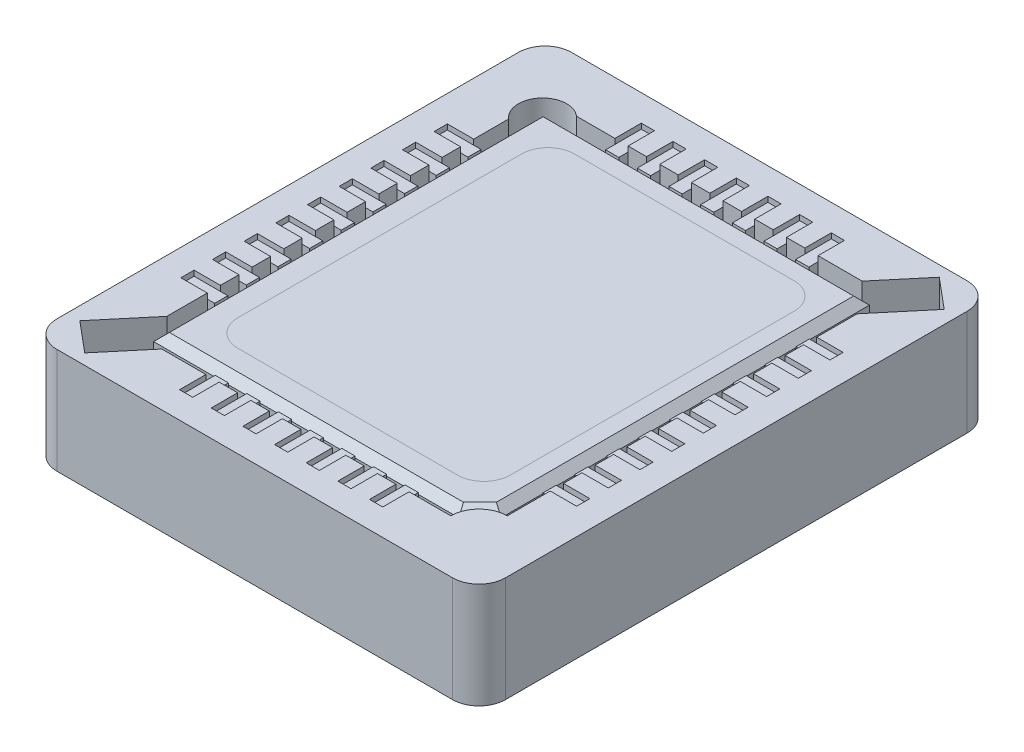
SolidWorks part; units mm, degrees
ref_plane "Alzado" through (0, 0, 0) normal (0, 0, 1) x (1, 0, 0)
ref_plane "Planta" through (0, 0, 0) normal (0, 1, 0) x (1, 0, 0)
ref_plane "Vista lateral" through (0, 0, 0) normal (1, 0, 0) x (0, 0, -1)
sketch "Croquis1" plane through (0, 0, 0) normal (0, 1, 0) x (1, 0, 0)
  line L0 (-6.5, -6.5829) -> (-8.0038, -8.3759)
  line L1 (-7.5, 9.75) -> (7.5, 9.75)
  line L2 (-8.5, 8.75) -> (-8.5, -8.75)
  line L3 (-7.5, -9.75) -> (7.5, -9.75)
  line L4 (8.5, 8.75) -> (8.5, -8.75)
  line L5 (-5.304, 7.75) -> (5.5211, 7.75)
  line L6 (-6.5, 6.3718) -> (-6.5, -6.5829)
  line L7 (-5.5211, -7.75) -> (5.4294, -7.75)
  line L8 (6.5, 6.5829) -> (6.5, -6.6794)
  line L9 (6.8545, 9.3398) -> (5.5211, 7.75)
  line L10 (8.0038, 8.3759) -> (6.5, 6.5829)
  line L11 (6.8545, 9.3398) -> (8.0038, 8.3759)
  line L12 (0, 0) -> (2.3031, -1.9317) construction
  line L13 (-8.0038, -8.3759) -> (-6.8545, -9.3398)
  line L14 (-5.5211, -7.75) -> (-6.8545, -9.3398)
  arc A0 (-7.5, 9.75) -> (-8.5, 8.75) centre (-7.5, 8.75) ccw
  arc A1 (7.5, 9.75) -> (8.5, 8.75) centre (7.5, 8.75) cw
  arc A2 (7.5, -9.75) -> (8.5, -8.75) centre (7.5, -8.75) ccw
  arc A3 (-8.5, -8.75) -> (-7.5, -9.75) centre (-7.5, -8.75) ccw
  arc A4 (6.5, -6.6794) -> (5.4294, -7.75) centre (6.5, -7.75) ccw
  arc A5 (-5.304, 7.75) -> (-6.5, 6.3718) centre (-5.902, 7.0609) ccw
  point P6 (-8.5, 9.75)
  point P9 (8.5, 9.75)
  point P14 (-8.5, -9.75)
  dimension "D5" = 1
  dimension "D1" = 17
  dimension "D2" = 19.5
  dimension "D3" = 8.5
  dimension "D4" = 9.75
  dimension "D6" = 2
  dimension "D7" = 2
  dimension "D8" = 2
  dimension "D9" = 2
  dimension "D12" = 90
extrude "Extruir1" add sketch "Croquis1" along normal blind 4
sketch "Croquis3" plane through (0, 4, 0) normal (0, 1, 0) x (-1, 0, 0)
  line L0 (-6.1479, 6.5628) -> (-5.3479, 7.3628)
  line L1 (-6.1479, -7.3996) -> (6.2216, -7.3996)
  line L2 (-6.1479, -7.3996) -> (-6.1479, 6.5628)
  line L3 (-5.3479, 7.3628) -> (6.2216, 7.3628)
  line L4 (6.2216, -7.3996) -> (6.2216, 7.3628)
  point P6 (-6.1479, 7.3628)
  dimension "D1" = 0.8
  dimension "D2" = 45
extrude "Extruir2" add sketch "Croquis3" against normal blind 4 separate body
chamfer "Chaflán1" distance 0.3 angle 45 5 edges at (-6.2216, 4, -0.0184) (-0.0368, 4, -7.3996) (6.1479, 4, -0.4184) (5.7479, 4, 6.9628) (-0.4368, 4, 7.3628)
sketch "Croquis4" plane through (0, 4, 0) normal (0, 1, 0) x (-1, 0, 0)
  line L1 (-4.2199, -6.4713) -> (4.1071, -6.4713)
  line L2 (-5.2199, -5.4713) -> (-5.2199, 5.2855)
  line L3 (-4.2199, 6.2855) -> (4.1071, 6.2855)
  line L4 (5.1071, -5.4713) -> (5.1071, 5.2855)
  arc A0 (-4.2199, -6.4713) -> (-5.2199, -5.4713) centre (-4.2199, -5.4713) cw
  arc A1 (-5.2199, 5.2855) -> (-4.2199, 6.2855) centre (-4.2199, 5.2855) cw
  arc A2 (4.1071, -6.4713) -> (5.1071, -5.4713) centre (4.1071, -5.4713) ccw
  arc A3 (4.1071, 6.2855) -> (5.1071, 5.2855) centre (4.1071, 5.2855) cw
  dimension "D1" = 1
split line "Línea de partición1"
sketch "Croquis5" plane through (0, 4, 0) normal (0, 1, 0) x (1, 0, 0)
  line L0 (6.5, -6.6794) -> (6.5, 6.5829) construction
  line L1 (6.5, 0.25) -> (7.5, 0.25)
  line L2 (6.5, 0.25) -> (6.5, -0.25)
  line L3 (6.5, -0.25) -> (7.5, -0.25)
  line L4 (7.5, 0.25) -> (7.5, -0.25)
  line L5 (8.5, 0) -> (10.2177, 0) construction
  line L6 (8.5, -8.75) -> (8.5, 8.75) construction
  line L7 (6.5, 1.45) -> (7.5, 1.45)
  line L8 (6.5, 1.45) -> (6.5, 0.95)
  line L9 (6.5, 0.95) -> (7.5, 0.95)
  line L10 (7.5, 1.45) -> (7.5, 0.95)
  line L11 (6.5, 2.65) -> (7.5, 2.65)
  line L12 (6.5, 2.65) -> (6.5, 2.15)
  line L13 (6.5, 2.15) -> (7.5, 2.15)
  line L14 (7.5, 2.65) -> (7.5, 2.15)
  line L15 (6.5, 3.85) -> (7.5, 3.85)
  line L16 (6.5, 3.85) -> (6.5, 3.35)
  line L17 (6.5, 3.35) -> (7.5, 3.35)
  line L18 (7.5, 3.85) -> (7.5, 3.35)
  line L19 (6.5, 5.05) -> (7.5, 5.05)
  line L20 (6.5, 5.05) -> (6.5, 4.55)
  line L21 (6.5, 4.55) -> (7.5, 4.55)
  line L22 (7.5, 5.05) -> (7.5, 4.55)
  line L23 (7.5, -5.05) -> (7.5, -4.55)
  line L24 (6.5, -4.55) -> (7.5, -4.55)
  line L25 (6.5, -5.05) -> (6.5, -4.55)
  line L26 (6.5, -5.05) -> (7.5, -5.05)
  line L27 (7.5, -3.85) -> (7.5, -3.35)
  line L28 (6.5, -3.35) -> (7.5, -3.35)
  line L29 (6.5, -3.85) -> (6.5, -3.35)
  line L30 (6.5, -3.85) -> (7.5, -3.85)
  line L31 (7.5, -2.65) -> (7.5, -2.15)
  line L32 (6.5, -2.15) -> (7.5, -2.15)
  line L33 (6.5, -2.65) -> (6.5, -2.15)
  line L34 (6.5, -2.65) -> (7.5, -2.65)
  line L35 (7.5, -1.45) -> (7.5, -0.95)
  line L36 (6.5, -0.95) -> (7.5, -0.95)
  line L37 (6.5, -1.45) -> (6.5, -0.95)
  line L38 (6.5, -1.45) -> (7.5, -1.45)
  line L39 (0, 9.75) -> (0, 11.4117) construction
  line L40 (7.5, 9.75) -> (-7.5, 9.75) construction
  line L41 (-6.5, -1.45) -> (-7.5, -1.45)
  line L42 (-6.5, -1.45) -> (-6.5, -0.95)
  line L43 (-6.5, -0.95) -> (-7.5, -0.95)
  line L44 (-7.5, -1.45) -> (-7.5, -0.95)
  line L45 (-6.5, -2.65) -> (-7.5, -2.65)
  line L46 (-6.5, -2.65) -> (-6.5, -2.15)
  line L47 (-6.5, -2.15) -> (-7.5, -2.15)
  line L48 (-7.5, -2.65) -> (-7.5, -2.15)
  line L49 (-6.5, -3.85) -> (-7.5, -3.85)
  line L50 (-6.5, -3.85) -> (-6.5, -3.35)
  line L51 (-6.5, -3.35) -> (-7.5, -3.35)
  line L52 (-7.5, -3.85) -> (-7.5, -3.35)
  line L53 (-6.5, -5.05) -> (-7.5, -5.05)
  line L54 (-6.5, -5.05) -> (-6.5, -4.55)
  line L55 (-6.5, -4.55) -> (-7.5, -4.55)
  line L56 (-7.5, -5.05) -> (-7.5, -4.55)
  line L57 (-7.5, 5.05) -> (-7.5, 4.55)
  line L58 (-6.5, 4.55) -> (-7.5, 4.55)
  line L59 (-6.5, 5.05) -> (-6.5, 4.55)
  line L60 (-6.5, 5.05) -> (-7.5, 5.05)
  line L61 (-7.5, 3.85) -> (-7.5, 3.35)
  line L62 (-6.5, 3.35) -> (-7.5, 3.35)
  line L63 (-6.5, 3.85) -> (-6.5, 3.35)
  line L64 (-6.5, 3.85) -> (-7.5, 3.85)
  line L65 (-7.5, 2.65) -> (-7.5, 2.15)
  line L66 (-6.5, 2.15) -> (-7.5, 2.15)
  line L67 (-6.5, 2.65) -> (-6.5, 2.15)
  line L68 (-6.5, 2.65) -> (-7.5, 2.65)
  line L69 (-7.5, 1.45) -> (-7.5, 0.95)
  line L70 (-6.5, 0.95) -> (-7.5, 0.95)
  line L71 (-6.5, 1.45) -> (-6.5, 0.95)
  line L72 (-6.5, 1.45) -> (-7.5, 1.45)
  line L73 (-7.5, 0.25) -> (-7.5, -0.25)
  line L74 (-6.5, -0.25) -> (-7.5, -0.25)
  line L75 (-6.5, 0.25) -> (-6.5, -0.25)
  line L76 (-6.5, 0.25) -> (-7.5, 0.25)
  line L77 (5.5211, 7.75) -> (-5.304, 7.75) construction
  line L78 (-0.25, 7.75) -> (0.25, 7.75)
  line L79 (-0.25, 7.75) -> (-0.25, 8.75)
  line L80 (-0.25, 8.75) -> (0.25, 8.75)
  line L81 (0.25, 7.75) -> (0.25, 8.75)
  line L82 (0.95, 7.75) -> (1.45, 7.75)
  line L83 (0.95, 7.75) -> (0.95, 8.75)
  line L84 (0.95, 8.75) -> (1.45, 8.75)
  line L85 (1.45, 7.75) -> (1.45, 8.75)
  line L86 (2.15, 7.75) -> (2.65, 7.75)
  line L87 (2.15, 7.75) -> (2.15, 8.75)
  line L88 (2.15, 8.75) -> (2.65, 8.75)
  line L89 (2.65, 7.75) -> (2.65, 8.75)
  line L90 (3.35, 7.75) -> (3.85, 7.75)
  line L91 (3.35, 7.75) -> (3.35, 8.75)
  line L92 (3.35, 8.75) -> (3.85, 8.75)
  line L93 (3.85, 7.75) -> (3.85, 8.75)
  line L94 (-3.85, 7.75) -> (-3.85, 8.75)
  line L95 (-3.35, 8.75) -> (-3.85, 8.75)
  line L96 (-3.35, 7.75) -> (-3.35, 8.75)
  line L97 (-3.35, 7.75) -> (-3.85, 7.75)
  line L98 (-2.65, 7.75) -> (-2.65, 8.75)
  line L99 (-2.15, 8.75) -> (-2.65, 8.75)
  line L100 (-2.15, 7.75) -> (-2.15, 8.75)
  line L101 (-2.15, 7.75) -> (-2.65, 7.75)
  line L102 (-1.45, 7.75) -> (-1.45, 8.75)
  line L103 (-0.95, 8.75) -> (-1.45, 8.75)
  line L104 (-0.95, 7.75) -> (-0.95, 8.75)
  line L105 (-0.95, 7.75) -> (-1.45, 7.75)
  line L106 (-0.95, -7.75) -> (-1.45, -7.75)
  line L107 (-0.95, -7.75) -> (-0.95, -8.75)
  line L108 (-0.95, -8.75) -> (-1.45, -8.75)
  line L109 (-1.45, -7.75) -> (-1.45, -8.75)
  line L110 (-2.15, -7.75) -> (-2.65, -7.75)
  line L111 (-2.15, -7.75) -> (-2.15, -8.75)
  line L112 (-2.15, -8.75) -> (-2.65, -8.75)
  line L113 (-2.65, -7.75) -> (-2.65, -8.75)
  line L114 (-3.35, -7.75) -> (-3.85, -7.75)
  line L115 (-3.35, -7.75) -> (-3.35, -8.75)
  line L116 (-3.35, -8.75) -> (-3.85, -8.75)
  line L117 (-3.85, -7.75) -> (-3.85, -8.75)
  line L118 (3.85, -7.75) -> (3.85, -8.75)
  line L119 (3.35, -8.75) -> (3.85, -8.75)
  line L120 (3.35, -7.75) -> (3.35, -8.75)
  line L121 (3.35, -7.75) -> (3.85, -7.75)
  line L122 (2.65, -7.75) -> (2.65, -8.75)
  line L123 (2.15, -8.75) -> (2.65, -8.75)
  line L124 (2.15, -7.75) -> (2.15, -8.75)
  line L125 (2.15, -7.75) -> (2.65, -7.75)
  line L126 (1.45, -7.75) -> (1.45, -8.75)
  line L127 (0.95, -8.75) -> (1.45, -8.75)
  line L128 (0.95, -7.75) -> (0.95, -8.75)
  line L129 (0.95, -7.75) -> (1.45, -7.75)
  line L130 (0.25, -7.75) -> (0.25, -8.75)
  line L131 (-0.25, -8.75) -> (0.25, -8.75)
  line L132 (-0.25, -7.75) -> (-0.25, -8.75)
  line L133 (-0.25, -7.75) -> (0.25, -7.75)
  dimension "D1" = 0.5
  dimension "D2" = 0.25
  dimension "D3" = 1
  dimension "D4" = 1
  dimension "D5" = 0.5
  dimension "D6" = 0.25
extrude "Cortar-Extruir1" cut sketch "Croquis5" against normal blind 3
sketch "Croquis6" plane through (0, 1, 0) normal (0, 1, 0) x (1, 0, 0)
  line L0 (-6.2216, 7.3996) -> (6.1479, 7.3996) construction
  line L1 (-3.85, 8.75) -> (-3.35, 8.75)
  line L2 (-3.85, 8.75) -> (-3.85, 7.3996)
  line L3 (-3.85, 7.3996) -> (-3.35, 7.3996)
  line L4 (-3.35, 8.75) -> (-3.35, 7.3996)
  line L5 (-2.65, 8.75) -> (-2.15, 8.75)
  line L6 (-2.65, 8.75) -> (-2.65, 7.3996)
  line L7 (-2.65, 7.3996) -> (-2.15, 7.3996)
  line L8 (-2.15, 8.75) -> (-2.15, 7.3996)
  line L9 (-1.45, 8.75) -> (-0.95, 8.75)
  line L10 (-1.45, 8.75) -> (-1.45, 7.3996)
  line L11 (-1.45, 7.3996) -> (-0.95, 7.3996)
  line L12 (-0.95, 8.75) -> (-0.95, 7.3996)
  line L13 (-0.25, 8.75) -> (0.25, 8.75)
  line L14 (-0.25, 8.75) -> (-0.25, 7.3996)
  line L15 (-0.25, 7.3996) -> (0.25, 7.3996)
  line L16 (0.25, 8.75) -> (0.25, 7.3996)
  line L17 (0.95, 8.75) -> (1.45, 8.75)
  line L18 (0.95, 8.75) -> (0.95, 7.3996)
  line L19 (0.95, 7.3996) -> (1.45, 7.3996)
  line L20 (1.45, 8.75) -> (1.45, 7.3996)
  line L21 (2.15, 8.75) -> (2.65, 8.75)
  line L22 (2.15, 8.75) -> (2.15, 7.3996)
  line L23 (2.15, 7.3996) -> (2.65, 7.3996)
  line L24 (2.65, 8.75) -> (2.65, 7.3996)
  line L25 (3.35, 8.75) -> (3.85, 8.75)
  line L26 (3.35, 8.75) -> (3.35, 7.3996)
  line L27 (3.35, 7.3996) -> (3.85, 7.3996)
  line L28 (3.85, 8.75) -> (3.85, 7.3996)
  line L29 (8.5, 0) -> (11.2679, 0) construction
  line L30 (8.5, -8.75) -> (8.5, 8.75) construction
  line L31 (3.85, -8.75) -> (3.85, -7.3996)
  line L32 (3.35, -7.3996) -> (3.85, -7.3996)
  line L33 (3.35, -8.75) -> (3.35, -7.3996)
  line L34 (3.35, -8.75) -> (3.85, -8.75)
  line L35 (2.65, -8.75) -> (2.65, -7.3996)
  line L36 (2.15, -7.3996) -> (2.65, -7.3996)
  line L37 (2.15, -8.75) -> (2.15, -7.3996)
  line L38 (2.15, -8.75) -> (2.65, -8.75)
  line L39 (1.45, -8.75) -> (1.45, -7.3996)
  line L40 (0.95, -7.3996) -> (1.45, -7.3996)
  line L41 (0.95, -8.75) -> (0.95, -7.3996)
  line L42 (0.95, -8.75) -> (1.45, -8.75)
  line L43 (0.25, -8.75) -> (0.25, -7.3996)
  line L44 (-0.25, -7.3996) -> (0.25, -7.3996)
  line L45 (-0.25, -8.75) -> (-0.25, -7.3996)
  line L46 (-0.25, -8.75) -> (0.25, -8.75)
  line L47 (-0.95, -8.75) -> (-0.95, -7.3996)
  line L48 (-1.45, -7.3996) -> (-0.95, -7.3996)
  line L49 (-1.45, -8.75) -> (-1.45, -7.3996)
  line L50 (-1.45, -8.75) -> (-0.95, -8.75)
  line L51 (-2.15, -8.75) -> (-2.15, -7.3996)
  line L52 (-2.65, -7.3996) -> (-2.15, -7.3996)
  line L53 (-2.65, -8.75) -> (-2.65, -7.3996)
  line L54 (-2.65, -8.75) -> (-2.15, -8.75)
  line L55 (-3.35, -8.75) -> (-3.35, -7.3996)
  line L56 (-3.85, -7.3996) -> (-3.35, -7.3996)
  line L57 (-3.85, -8.75) -> (-3.85, -7.3996)
  line L58 (-3.85, -8.75) -> (-3.35, -8.75)
  line L59 (-6.2216, -7.3628) -> (-6.2216, 7.3996) construction
  line L60 (-7.5, 5.05) -> (-6.2216, 5.05)
  line L61 (-7.5, 5.05) -> (-7.5, 4.55)
  line L62 (-7.5, 4.55) -> (-6.2216, 4.55)
  line L63 (-6.2216, 5.05) -> (-6.2216, 4.55)
  line L64 (-7.5, 3.85) -> (-6.2216, 3.85)
  line L65 (-7.5, 3.85) -> (-7.5, 3.35)
  line L66 (-7.5, 3.35) -> (-6.2216, 3.35)
  line L67 (-6.2216, 3.85) -> (-6.2216, 3.35)
  line L68 (-7.5, 2.65) -> (-6.2216, 2.65)
  line L69 (-7.5, 2.65) -> (-7.5, 2.15)
  line L70 (-7.5, 2.15) -> (-6.2216, 2.15)
  line L71 (-6.2216, 2.65) -> (-6.2216, 2.15)
  line L72 (-7.5, 1.45) -> (-6.2216, 1.45)
  line L73 (-7.5, 1.45) -> (-7.5, 0.95)
  line L74 (-7.5, 0.95) -> (-6.2216, 0.95)
  line L75 (-6.2216, 1.45) -> (-6.2216, 0.95)
  line L76 (-7.5, 0.25) -> (-6.2216, 0.25)
  line L77 (-7.5, 0.25) -> (-7.5, -0.25)
  line L78 (-7.5, -0.25) -> (-6.2216, -0.25)
  line L79 (-6.2216, 0.25) -> (-6.2216, -0.25)
  line L80 (-7.5, -0.95) -> (-6.2216, -0.95)
  line L81 (-7.5, -0.95) -> (-7.5, -1.45)
  line L82 (-7.5, -1.45) -> (-6.2216, -1.45)
  line L83 (-6.2216, -0.95) -> (-6.2216, -1.45)
  line L84 (-7.5, -2.15) -> (-6.2216, -2.15)
  line L85 (-7.5, -2.15) -> (-7.5, -2.65)
  line L86 (-7.5, -2.65) -> (-6.2216, -2.65)
  line L87 (-6.2216, -2.15) -> (-6.2216, -2.65)
  line L88 (-7.5, -3.35) -> (-6.2216, -3.35)
  line L89 (-7.5, -3.35) -> (-7.5, -3.85)
  line L90 (-7.5, -3.85) -> (-6.2216, -3.85)
  line L91 (-6.2216, -3.35) -> (-6.2216, -3.85)
  line L92 (-7.5, -4.55) -> (-6.2216, -4.55)
  line L93 (-7.5, -4.55) -> (-7.5, -5.05)
  line L94 (-7.5, -5.05) -> (-6.2216, -5.05)
  line L95 (-6.2216, -4.55) -> (-6.2216, -5.05)
  line L96 (0, -9.75) -> (0, -10.9933) construction
  line L97 (-7.5, -9.75) -> (7.5, -9.75) construction
  line L98 (6.2216, -4.55) -> (6.2216, -5.05)
  line L99 (7.5, -5.05) -> (6.2216, -5.05)
  line L100 (7.5, -4.55) -> (7.5, -5.05)
  line L101 (7.5, -4.55) -> (6.2216, -4.55)
  line L102 (6.2216, -3.35) -> (6.2216, -3.85)
  line L103 (7.5, -3.85) -> (6.2216, -3.85)
  line L104 (7.5, -3.35) -> (7.5, -3.85)
  line L105 (7.5, -3.35) -> (6.2216, -3.35)
  line L106 (6.2216, -2.15) -> (6.2216, -2.65)
  line L107 (7.5, -2.65) -> (6.2216, -2.65)
  line L108 (7.5, -2.15) -> (7.5, -2.65)
  line L109 (7.5, -2.15) -> (6.2216, -2.15)
  line L110 (6.2216, -0.95) -> (6.2216, -1.45)
  line L111 (7.5, -1.45) -> (6.2216, -1.45)
  line L112 (7.5, -0.95) -> (7.5, -1.45)
  line L113 (7.5, -0.95) -> (6.2216, -0.95)
  line L114 (6.2216, 0.25) -> (6.2216, -0.25)
  line L115 (7.5, -0.25) -> (6.2216, -0.25)
  line L116 (7.5, 0.25) -> (7.5, -0.25)
  line L117 (7.5, 0.25) -> (6.2216, 0.25)
  line L118 (6.2216, 1.45) -> (6.2216, 0.95)
  line L119 (7.5, 0.95) -> (6.2216, 0.95)
  line L120 (7.5, 1.45) -> (7.5, 0.95)
  line L121 (7.5, 1.45) -> (6.2216, 1.45)
  line L122 (6.2216, 2.65) -> (6.2216, 2.15)
  line L123 (7.5, 2.15) -> (6.2216, 2.15)
  line L124 (7.5, 2.65) -> (7.5, 2.15)
  line L125 (7.5, 2.65) -> (6.2216, 2.65)
  line L126 (6.2216, 3.85) -> (6.2216, 3.35)
  line L127 (7.5, 3.35) -> (6.2216, 3.35)
  line L128 (7.5, 3.85) -> (7.5, 3.35)
  line L129 (7.5, 3.85) -> (6.2216, 3.85)
  line L130 (6.2216, 5.05) -> (6.2216, 4.55)
  line L131 (7.5, 4.55) -> (6.2216, 4.55)
  line L132 (7.5, 5.05) -> (7.5, 4.55)
  line L133 (7.5, 5.05) -> (6.2216, 5.05)
extrude "Extruir3" add sketch "Croquis6" along normal blind 2.8 separate body
